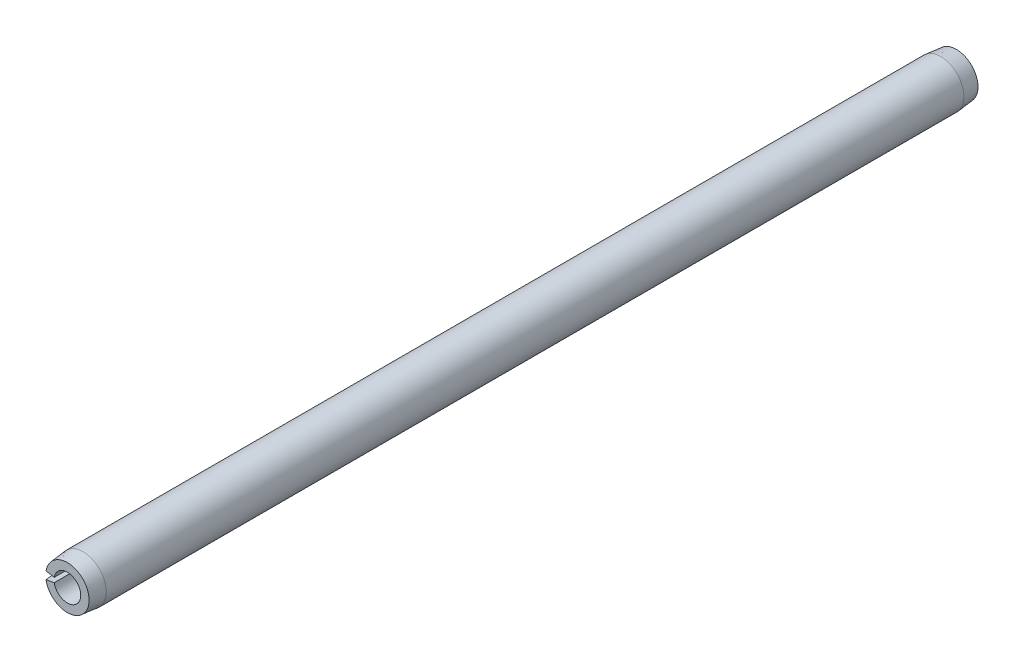
SolidWorks part; units mm, degrees
ref_plane "Front Plane" through (0, 0, 0) normal (0, 0, 1) x (1, 0, 0)
ref_plane "Top Plane" through (0, 0, 0) normal (0, 1, 0) x (1, 0, 0)
ref_plane "Right Plane" through (0, 0, 0) normal (1, 0, 0) x (0, 0, -1)
sketch "Sketch1" plane through (0, 0, 0) normal (0, 0, 1) x (1, 0, 0)
  line L0 (0.9525, 0) -> (1.6637, 0) construction
  line L1 (-1.6384, 0.2889) -> (-0.938, 0.1654)
  line L2 (-0.938, -0.1654) -> (-1.6384, -0.2889)
  arc A0 (-1.6384, -0.2889) -> (-1.6384, 0.2889) centre (0, 0) ccw
  arc A1 (-0.938, -0.1654) -> (-0.938, 0.1654) centre (0, 0) ccw
  dimension "OD" = 3.3274
  dimension "Wall thickness" = 0.7112
  dimension "D3" = 20
extrude "Extrude1" add sketch "Sketch1" along normal mid plane 63.5
sketch "Sketch2" plane through (0, 0, 0) normal (1, 0, 0) x (0, 0, -1)
  line L0 (0, -1.6637) -> (0, 1.6637) construction
  line L1 (31.75, 0) -> (-31.75, 0) construction
  line L2 (31.75, -0.9525) -> (31.75, 0.9525) construction
  line L3 (31.75, 1.6637) -> (-31.75, 1.6637) construction
  line L4 (31.75, 1.6637) -> (31.75, 1.5494)
  line L5 (31.75, 1.5494) -> (30.6324, 1.6637)
  line L6 (30.6324, 1.6637) -> (31.75, 1.6637)
  line L7 (31.75, -1.6637) -> (31.75, 1.6637) construction
  line L8 (-30.6324, 1.6637) -> (-31.75, 1.6637)
  line L9 (-31.75, 1.5494) -> (-30.6324, 1.6637)
  line L10 (-31.75, 1.6637) -> (-31.75, 1.5494)
  line L11 (30.6324, -1.6637) -> (31.75, -1.6637) construction
  line L12 (31.75, -1.5494) -> (30.6324, -1.6637) construction
  line L13 (31.75, -1.6637) -> (31.75, -1.5494) construction
  dimension "B" = 3.0988
  dimension "Chamfer max" = 1.1176
revolve "Cut-Revolve1" cut sketch "Sketch2" angle 360 about L1
sketch "Sketch3" plane through (0, 0, 0) normal (0, 0, 1) x (1, 0, 0)
  line L0 (0.9525, 0) -> (1.6637, 0) construction
  line L1 (0.9525, 0) -> (1.6637, 0)
  circle A0 centre (0, 0) radius 1.6637
  circle A1 centre (0, 0) radius 0.9525
  arc A2 (-1.6384, -0.2889) -> (-1.6384, 0.2889) centre (0, 0) ccw construction
  arc A3 (-0.938, -0.1654) -> (-0.938, 0.1654) centre (0, 0) ccw construction
